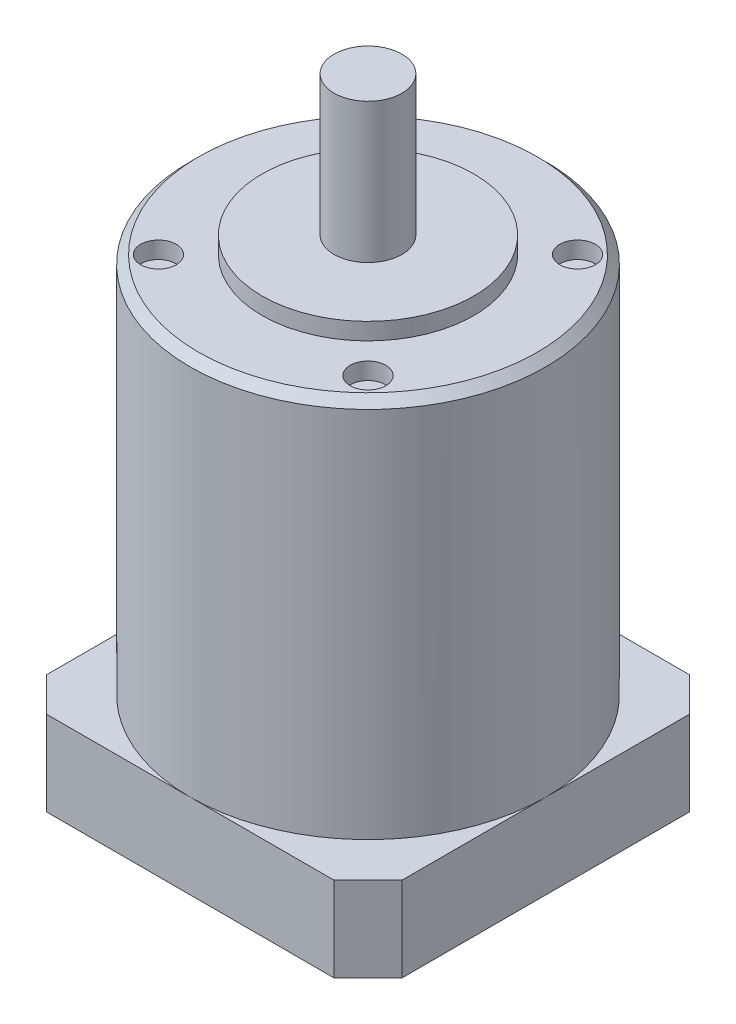
SolidWorks part; units mm, degrees
ref_plane "Front" through (0, 0, 0) normal (0, 0, 1) x (1, 0, 0)
ref_plane "Top" through (0, 0, 0) normal (0, 1, 0) x (1, 0, 0)
ref_plane "Right" through (0, 0, 0) normal (1, 0, 0) x (0, 0, -1)
sketch "草圖1" plane through (0, 0, 0) normal (0, 1, 0) x (1, 0, 0)
  line L1 (-21, -21) -> (21, -21)
  line L2 (-21, -21) -> (-21, 21)
  line L3 (-21, 21) -> (21, 21)
  line L4 (21, -21) -> (21, 21)
  line L5 (-21, -21) -> (21, 21) construction
  line L6 (-21, 21) -> (21, -21) construction
  point P0 (0, 0)
  dimension "D1" = 42
extrude "填料-伸長1" add sketch "草圖1" along normal blind 10
sketch "草圖2" plane through (0, 10, 0) normal (0, 1, 0) x (1, 0, 0)
  circle A0 centre (0, 0) radius 21
extrude "填料-伸長2" add sketch "草圖2" along normal blind 45
sketch "草圖3" plane through (0, 55, 0) normal (0, 1, 0) x (1, 0, 0)
  circle A0 centre (0, 0) radius 4
  dimension "D1" = 8
extrude "填料-伸長3" add sketch "草圖3" along normal blind 18.5
chamfer "導角1" distance 4 angle 45 4 edges at (21, 5, -21) (-21, 5, -21) (-21, 5, 21) (21, 5, 21)
sketch "草圖4" plane through (0, 0, 0) normal (0, -1, 0) x (1, 0, 0)
  circle A0 centre (0, 0) radius 11
  dimension "D1" = 22
extrude "除料-伸長1" cut sketch "草圖4" against normal blind 25
sketch "草圖5" plane through (0, 55, 0) normal (0, 1, 0) x (1, 0, 0)
  circle A0 centre (0, 0) radius 12.5
  dimension "D1" = 25
extrude "填料-伸長4" add sketch "草圖5" along normal blind 2
chamfer "導角2" distance 1 angle 45 1 edges at (0, 55, 21)
sketch "草圖6" plane through (0, 55, 0) normal (0, 1, 0) x (1, 0, 0)
  line L0 (-12.3744, 12.3744) -> (0, 0) construction
  circle A0 centre (-12.3744, 12.3744) radius 2.1
  dimension "D2" = 4.2
  dimension "D1" = 17.5
extrude "除料-伸長2" cut sketch "草圖6" against normal blind 2
pattern_circular "環狀複製排列1" count 4 over 360 about axis through (0, 0, 0) along (0, 1, 0) of "除料-伸長2"
sketch "草圖7" plane through (0, 0, 0) normal (0, -1, 0) x (1, 0, 0)
  line L0 (0, 0) -> (0, 15.5) construction
  line L1 (0, 15.5) -> (-15.5, 15.5) construction
  circle A0 centre (-15.5, 15.5) radius 2.1
  dimension "D2" = 4.2
  dimension "D1" = 15.5
extrude "除料-伸長3" cut sketch "草圖7" against normal blind 8
pattern_circular "環狀複製排列2" count 4 over 360 about axis through (0, 0, 0) along (0, 1, 0) of "除料-伸長3"
